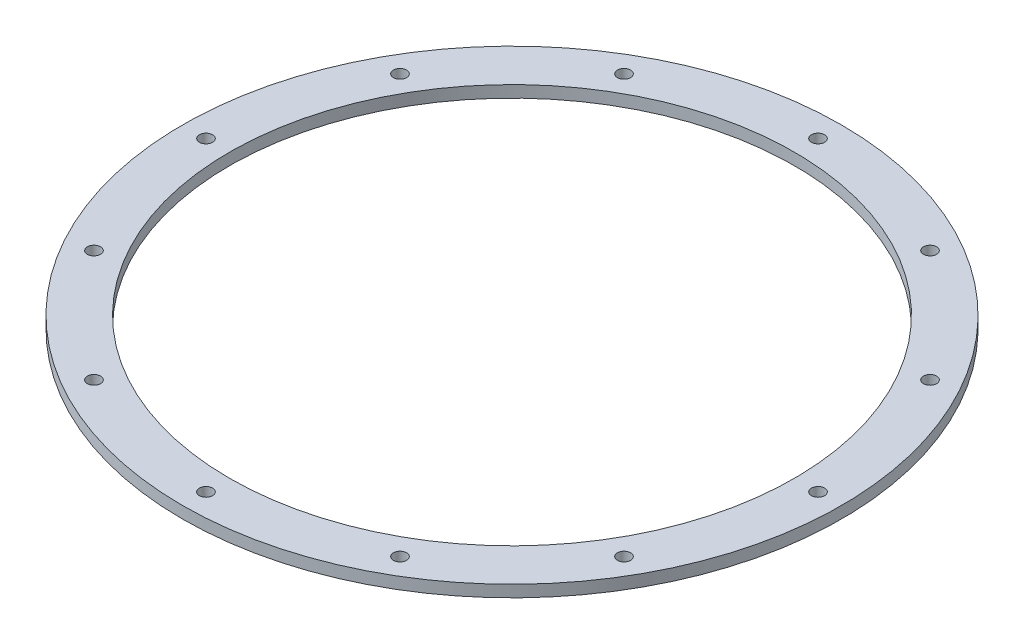
SolidWorks part; units mm, degrees
material "PTFE (general)"
ref_plane "Front Plane" through (0, 0, 0) normal (0, 0, 1) x (1, 0, 0)
ref_plane "Top Plane" through (0, 0, 0) normal (0, 1, 0) x (1, 0, 0)
ref_plane "Right Plane" through (0, 0, 0) normal (1, 0, 0) x (0, 0, -1)
ref_axis "Axis1" through (0, 55, 0) along (0, -1, 0)
sketch "Sketch1" plane through (0, 0, 0) normal (0, 0, 1) x (1, 0, 0)
  line L0 (-38.1, 0) -> (0, 0) construction
  line L1 (-38.1, 0) -> (-44.45, 0)
  line L2 (-38.1, 0) -> (-38.1, 1.5875)
  line L3 (-38.1, 1.5875) -> (-44.45, 1.5875)
  line L4 (-44.45, 0) -> (-44.45, 1.5875)
  line L7 (0, 1.5875) -> (-38.1, 1.5875) construction
  point P1 (-44.45, 1.5875)
  point P2 (-38.1, 1.5875)
  point P3 (-44.45, 0)
  point P9 (-44.3942, 0)
  point P12 (-44.45, 0)
  point P13 (-44.45, 1.526)
  point P14 (-38.1207, 0)
  point P15 (-38.1, 0.0188)
  point P18 (-38.1, 1.5875)
  point P21 (-38.1, 1.5582)
revolve "Main" add sketch "Sketch1" angle 360 about axis through (0, 55, 0) along (0, -1, 0)
sketch "Hole Location" plane through (0, 0, 0) normal (0, 1, 0) x (1, 0, 0)
  line L0 (0, 0) -> (-41.275, 0) construction
  circle A0 centre (0, 0) radius 41.275 construction
  dimension "D1" = 82.55
hole_wizard "#50 (0.07) Diameter Hole1" positions "Sketch3" profile "Sketch5" hole size "#50" standard "ANSI Inch" end condition through all
sketch "Sketch3" plane through (0, 0, 0) normal (0, -1, 0) x (-1, 0, 0)
  point P0 (41.275, 0)
sketch "Sketch5" plane through (-41.275, 0, 0) normal (1, 0, 0) x (0, 0, -1)
  line L0 (0, 0) -> (0, 1.5875)
  line L1 (0, 1.5875) -> (0.889, 1.5875)
  line L2 (0.889, 1.5875) -> (0.889, 0)
  line L5 (0.889, 0) -> (0, 0)
  line L11 (0, -6.35) -> (0, 107.95) construction
  dimension "Thru Hole Dia." = 1.778
  dimension "Thru Hole Depth" = 1.5875
pattern_circular "Screw Passthroughs" count 12 over 360 about axis through (0, 0, 0) along (0, 1, 0) of "#50 (0.07) Diameter Hole1"
equation "\"D1@Hole Location\"=\"TANK DIAMETER@Cryo Tank.Assembly\"+\"GASKET SEAT THICKNESS@Cryo Tank.Assembly\""
